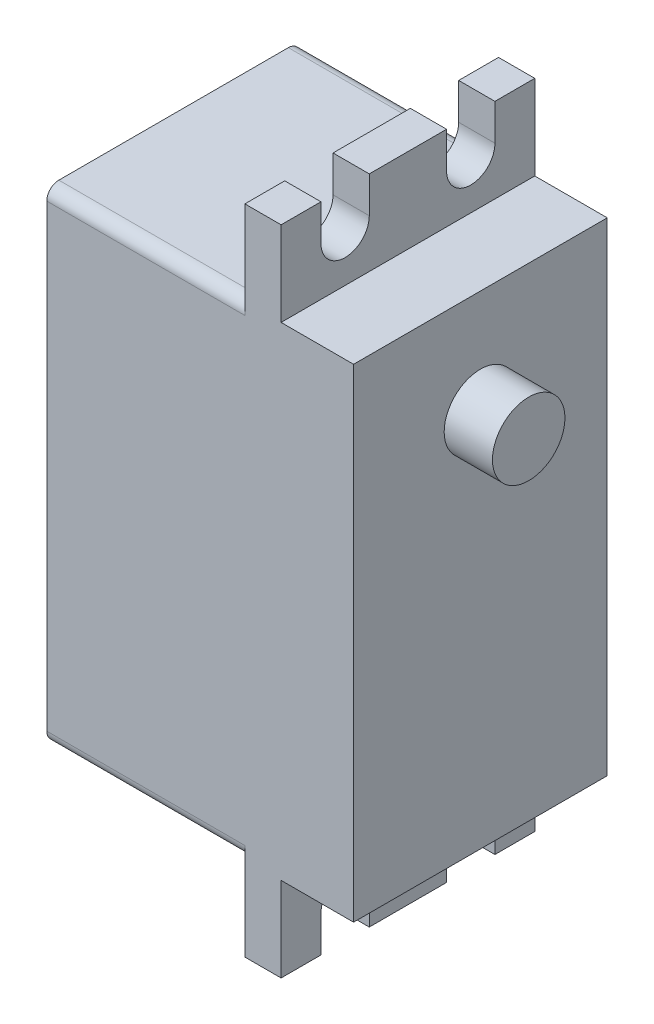
SolidWorks part; units mm, degrees
material "Cast Alloy Steel"
ref_plane "Front Plane" through (0, 0, 0) normal (0, 0, 1) x (1, 0, 0)
ref_plane "Top Plane" through (0, 0, 0) normal (0, 1, 0) x (1, 0, 0)
ref_plane "Right Plane" through (0, 0, 0) normal (1, 0, 0) x (0, 0, -1)
sketch "Sketch1" plane through (0, 0, 0) normal (1, 0, 0) x (0, 0, -1)
  line L1 (-10.5, 20) -> (10.5, 20)
  line L2 (-10.5, 20) -> (-10.5, -20)
  line L3 (-10.5, -20) -> (10.5, -20)
  line L4 (10.5, 20) -> (10.5, -20)
  line L5 (-10.5, 20) -> (10.5, -20) construction
  line L6 (-10.5, -20) -> (10.5, 20) construction
  point P0 (0, 0)
  dimension "D1" = 21
  dimension "D2" = 40
extrude "Boss-Extrude1" add sketch "Sketch1" along normal blind 16.4
sketch "Sketch2" plane through (16.4, 0, 0) normal (1, 0, 0) x (0, 0, -1)
  line L0 (10.5, -20) -> (10.5, 20) construction
  line L1 (-10.5, -27) -> (10.5, -27)
  line L2 (-10.5, -27) -> (-10.5, 27)
  line L3 (-10.5, 27) -> (10.5, 27)
  line L4 (10.5, -27) -> (10.5, 27)
  line L5 (-10.5, -27) -> (10.5, 27) construction
  line L6 (-10.5, 27) -> (10.5, -27) construction
  point P0 (0, 0)
  dimension "D1" = 54
extrude "Boss-Extrude2" add sketch "Sketch2" along normal blind 3
sketch "Sketch3" plane through (19.4, 0, 0) normal (1, 0, 0) x (0, 0, -1)
  line L0 (-3.2, 24) -> (-3.2, 27)
  line L1 (10.5, 27) -> (-10.5, 27) construction
  line L2 (-7.2, 24) -> (-7.2, 27)
  line L3 (-7.2, 27) -> (-3.2, 27)
  arc A0 (-3.2, 24) -> (-7.2, 24) centre (-5.2, 24) cw
  point P2 (-5.2, 22)
  dimension "D2" = 4
  dimension "D1" = 5.2
  dimension "D3" = 5
extrude "Cut-Extrude1" cut sketch "Sketch3" against normal up to next (3 mm away)
mirror "Mirror1" about plane through (0, 0, 0) normal (0, 0, 1) of "Cut-Extrude1"
mirror "Mirror2" about plane through (0, 0, 0) normal (0, 1, 0) of "Mirror1", "Cut-Extrude1"
sketch "Sketch5" plane through (19.4, 0, 0) normal (1, 0, 0) x (0, 0, -1)
  line L0 (10.5, -27) -> (10.5, 27) construction
  line L1 (-10.5, -20) -> (10.5, -20)
  line L2 (-10.5, -20) -> (-10.5, 20)
  line L3 (-10.5, 20) -> (10.5, 20)
  line L4 (10.5, -20) -> (10.5, 20)
  line L5 (-10.5, -20) -> (10.5, 20) construction
  line L6 (-10.5, 20) -> (10.5, -20) construction
  line L7 (10.5, 20) -> (-10.5, 20) construction
  point P0 (0, 0)
extrude "Boss-Extrude4" add sketch "Sketch5" along normal blind 6
sketch "Sketch6" plane through (25.4, 0, 0) normal (1, 0, 0) x (0, 0, -1)
  line L0 (-10.5, -20) -> (10.5, -20) construction
  circle A0 centre (0, 11.4) radius 3
  dimension "D1" = 31.4
  dimension "D2" = 6
extrude "Boss-Extrude5" add sketch "Sketch6" along normal blind 0.01
fillet "Fillet1" radius 1 4 edges at (8.2, -20, 10.5) (8.2, -20, -10.5) (8.2, 20, 10.5) (8.2, 20, -10.5)
sketch "Sketch9" plane through (25.41, 0, 0) normal (1, 0, 0) x (0, 0, -1)
  circle A0 centre (0, 11.4) radius 3
  circle A1 centre (0, 11.4) radius 3 construction
extrude "Boss-Extrude7" add sketch "Sketch9" along normal blind 3.9878
